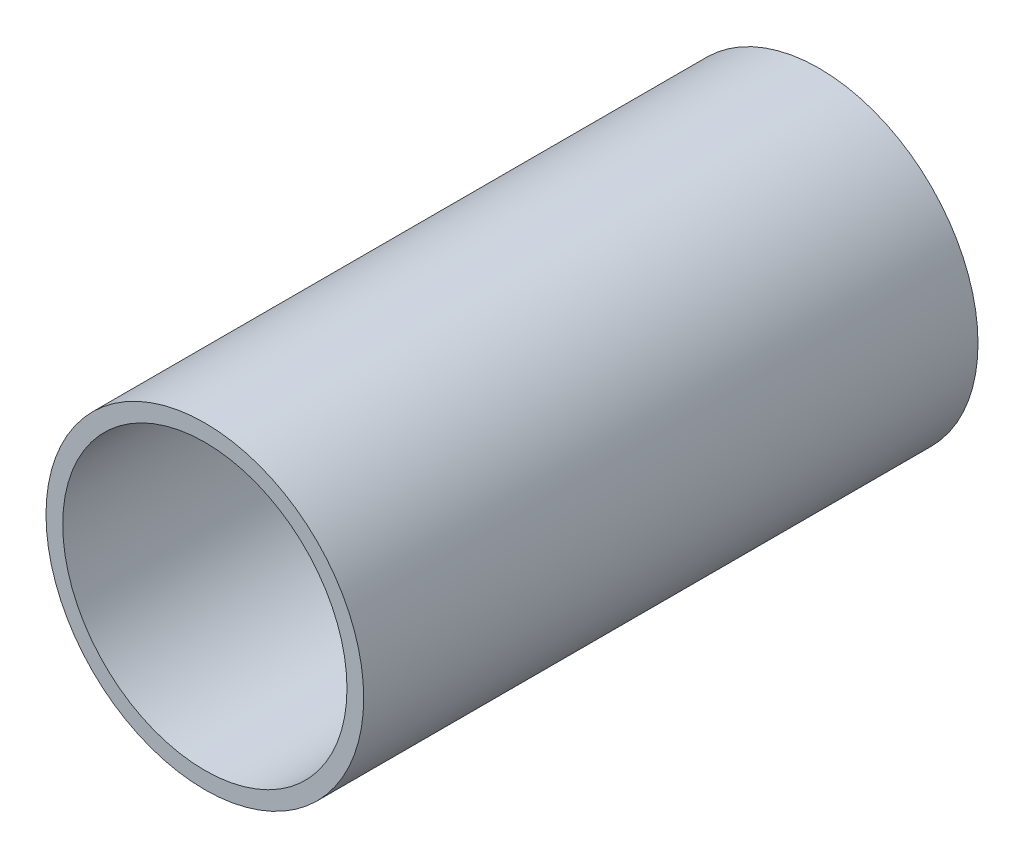
SolidWorks part; units mm, degrees
material "PVC Rigid"
ref_plane "Front Plane" through (0, 0, 0) normal (0, 0, 1) x (1, 0, 0)
ref_plane "Top Plane" through (0, 0, 0) normal (0, 1, 0) x (1, 0, 0)
ref_plane "Right Plane" through (0, 0, 0) normal (1, 0, 0) x (0, 0, -1)
sketch "Sketch1" plane through (0, 0, 0) normal (0, 0, 1) x (1, 0, 0)
  circle A0 centre (0, 0) radius 57.15
  dimension "Pipe OD" = 114.3
extrude "Extrude-Thin1" add sketch "Sketch1" along normal mid plane 221 thin thin type one direction reverse wall 6.0198
